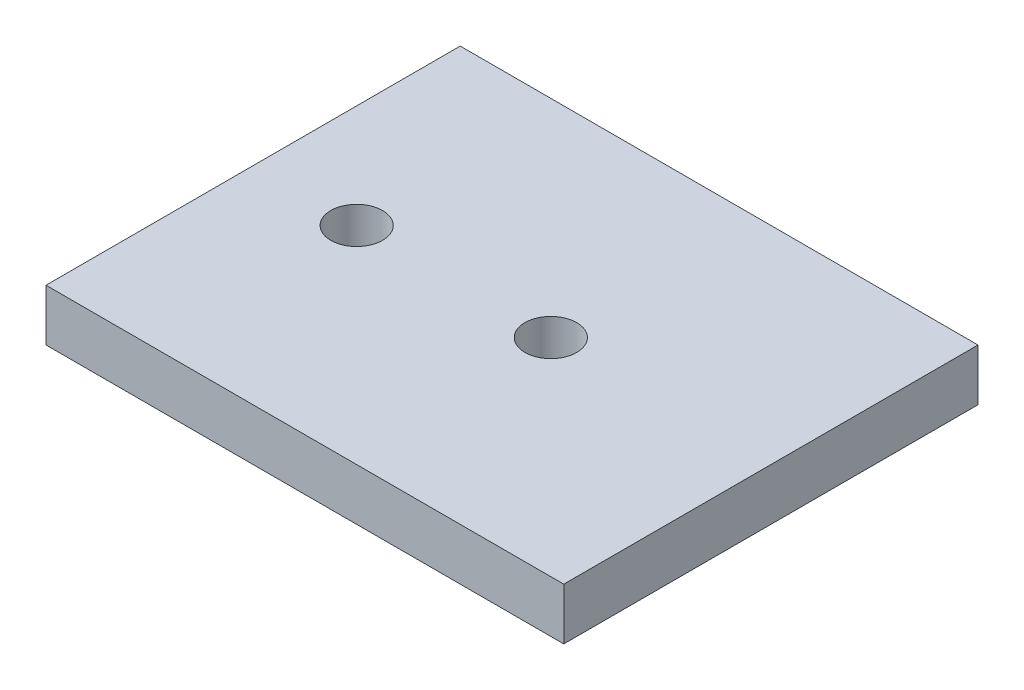
SolidWorks part; units mm, degrees
ref_plane "Front Plane" through (0, 0, 0) normal (0, 0, 1) x (1, 0, 0)
ref_plane "Top Plane" through (0, 0, 0) normal (0, 1, 0) x (1, 0, 0)
ref_plane "Right Plane" through (0, 0, 0) normal (1, 0, 0) x (0, 0, -1)
sketch "Sketch2" plane through (0, 0, 0) normal (0, 1, 0) x (1, 0, 0)
  line L1 (-63.5, -50.8) -> (63.5, -50.8)
  line L2 (-63.5, -50.8) -> (-63.5, 50.8)
  line L3 (-63.5, 50.8) -> (63.5, 50.8)
  line L4 (63.5, -50.8) -> (63.5, 50.8)
  line L5 (-63.5, -50.8) -> (63.5, 50.8) construction
  line L6 (-63.5, 50.8) -> (63.5, -50.8) construction
  point P0 (0, 0)
  dimension "D1" = 101.6
  dimension "D2" = 127
extrude "Boss-Extrude1" add sketch "Sketch2" along normal blind 12.7
sketch "Sketch3" plane through (0, 12.7, 0) normal (0, 1, 0) x (1, 0, 0)
  line L0 (-63.5, 50.8) -> (-63.5, -50.8) construction
  line L1 (63.5, 50.8) -> (-63.5, 50.8) construction
  line L2 (-38.1, 0) -> (9.525, 0) construction
  circle A0 centre (-38.1, 0) radius 6.35
  circle A1 centre (9.525, 0) radius 6.35
  dimension "D1" = 12.7
  dimension "D2" = 47.625
  dimension "D3" = 25.4
  dimension "D4" = 50.8
extrude "Cut-Extrude1" cut sketch "Sketch3" against normal through all
